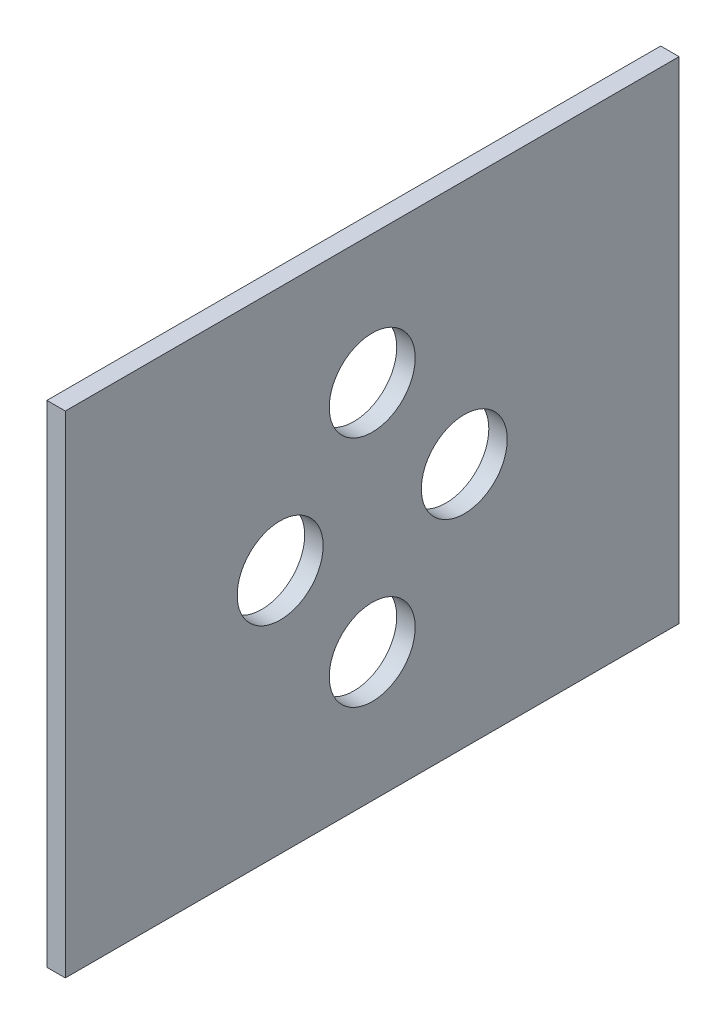
SolidWorks part; units mm, degrees
ref_plane "Płaszczyzna przednia" through (0, 0, 0) normal (0, 0, 1) x (1, 0, 0)
ref_plane "Płaszczyzna górna" through (0, 0, 0) normal (0, 1, 0) x (1, 0, 0)
ref_plane "Płaszczyzna prawa" through (0, 0, 0) normal (1, 0, 0) x (0, 0, -1)
sketch "Sketch1" plane through (0, 0, 0) normal (1, 0, 0) x (0, 0, -1)
  line L1 (-25, -20) -> (25, -20)
  line L2 (-25, -20) -> (-25, 20)
  line L3 (-25, 20) -> (25, 20)
  line L4 (25, -20) -> (25, 20)
  line L5 (-25, -20) -> (25, 20) construction
  line L6 (-25, 20) -> (25, -20) construction
  point P0 (0, 0)
  dimension "D1" = 40
  dimension "D2" = 50
extrude "Boss-Extrude1" add sketch "Sketch1" along normal blind 1.5
sketch "Sketch2" plane through (1.5, 0, 0) normal (1, 0, 0) x (0, 0, -1)
  line L0 (0, -20) -> (0, 20) construction
  line L1 (-25, -20) -> (25, -20) construction
  line L2 (25, 20) -> (-25, 20) construction
  line L3 (0, 20) -> (25, 0) construction
  line L4 (25, -20) -> (25, 20) construction
  line L5 (25, 0) -> (-25, 0) construction
  line L6 (-25, 20) -> (-25, -20) construction
  circle A0 centre (0, 9.5) radius 3.5
  circle A1 centre (0, -9.5) radius 3.5
  circle A2 centre (7.5, 0) radius 3.5
  circle A3 centre (-7.5, 0) radius 3.5
  dimension "D1" = 7.5
  dimension "D2" = 15
  dimension "D3" = 9.5
  dimension "D4" = 19
extrude "Cut-Extrude1" cut sketch "Sketch2" against normal blind 11.5
